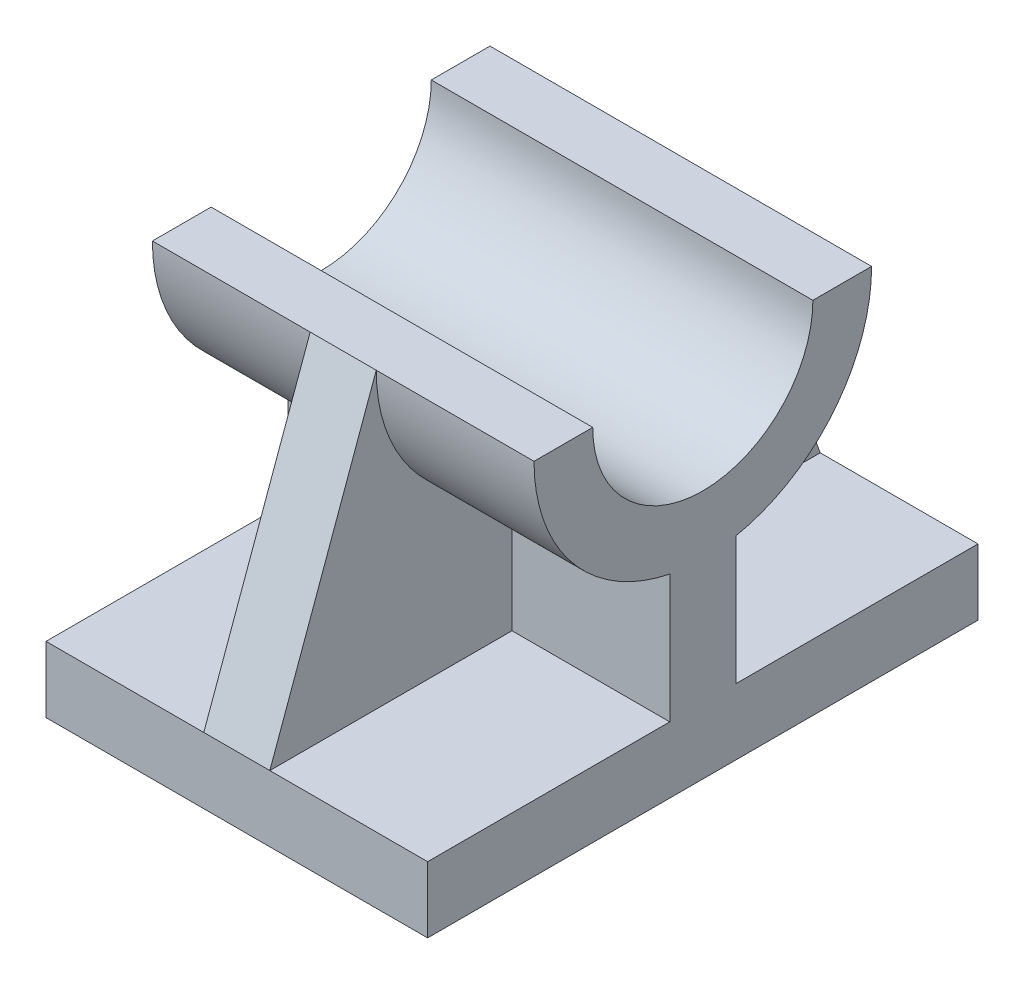
SolidWorks part; units mm, degrees
ref_plane "Front Plane" through (0, 0, 0) normal (0, 0, 1) x (1, 0, 0)
ref_plane "Top Plane" through (0, 0, 0) normal (0, 1, 0) x (1, 0, 0)
ref_plane "Right Plane" through (0, 0, 0) normal (1, 0, 0) x (0, 0, -1)
sketch "Sketch1" plane through (0, 0, 0) normal (1, 0, 0) x (0, 0, -1)
  line L0 (0, 0) -> (0, 44.5) construction
  line L1 (-23, 44.5) -> (-15, 44.5)
  line L2 (-37.5, -4.5) -> (37.5, -4.5)
  line L3 (-37.5, -4.5) -> (-37.5, 4.5)
  line L4 (-37.5, 4.5) -> (-4.5, 4.5)
  line L5 (37.5, -4.5) -> (37.5, 4.5)
  line L8 (15, 44.5) -> (23, 44.5)
  line L9 (4.5, 4.5) -> (37.5, 4.5)
  line L11 (-4.5, 21.9445) -> (-4.5, 4.5)
  line L13 (4.5, 21.9445) -> (4.5, 4.5)
  arc A0 (-15, 44.5) -> (15, 44.5) centre (0, 44.5) ccw
  arc A1 (-23, 44.5) -> (-4.5, 21.9445) centre (0, 44.5) ccw
  arc A2 (4.5, 21.9445) -> (23, 44.5) centre (0, 44.5) ccw
  point P7 (0, 12.3207)
  point P12 (0, 0)
  dimension "D4" = 46
  dimension "D5" = 30
  dimension "D1" = 9
  dimension "D2" = 75
  dimension "D3" = 44.5
  dimension "D6" = 4.5
  dimension "D7" = 17.4445
  dimension "D8" = 4.5
extrude "Boss-Extrude1" add sketch "Sketch1" along normal mid plane 52
sketch "Sketch6" plane through (0, 0, 0) normal (1, 0, 0) x (0, 0, -1)
  line L0 (23, 44.5) -> (37.5, 4.5)
rib "Rib9" sketch "Sketch6" sketch "Sketch6" thickness 9 extrusion direction parallel to sketch draft on no parameters "D1"=9
mirror "Mirror1" about plane through (0, 0, 0) normal (0, 0, 1) of "Rib9"
